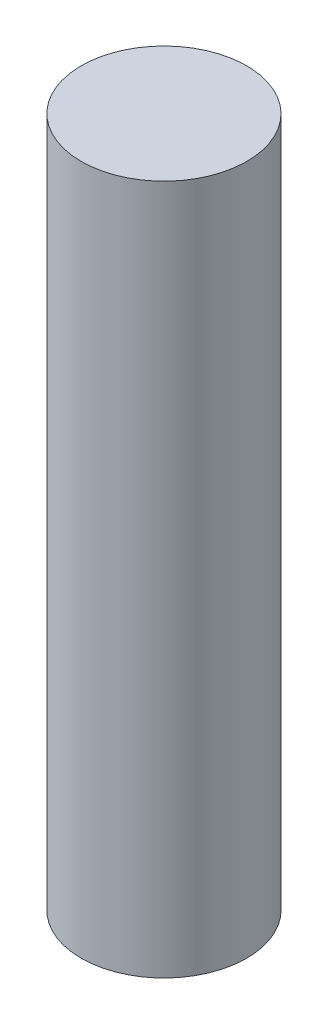
SolidWorks part; units mm, degrees
ref_plane "Front" through (0, 0, 0) normal (0, 0, 1) x (1, 0, 0)
ref_plane "Top" through (0, 0, 0) normal (0, 1, 0) x (1, 0, 0)
ref_plane "Right" through (0, 0, 0) normal (1, 0, 0) x (0, 0, -1)
sketch "Sketch1" plane through (0, 0, 0) normal (0, 1, 0) x (1, 0, 0)
  circle A0 centre (0, 0) radius 1.5
  dimension "D1" = 3
extrude "Boss-Extrude1" add sketch "Sketch1" along normal blind 12.5
